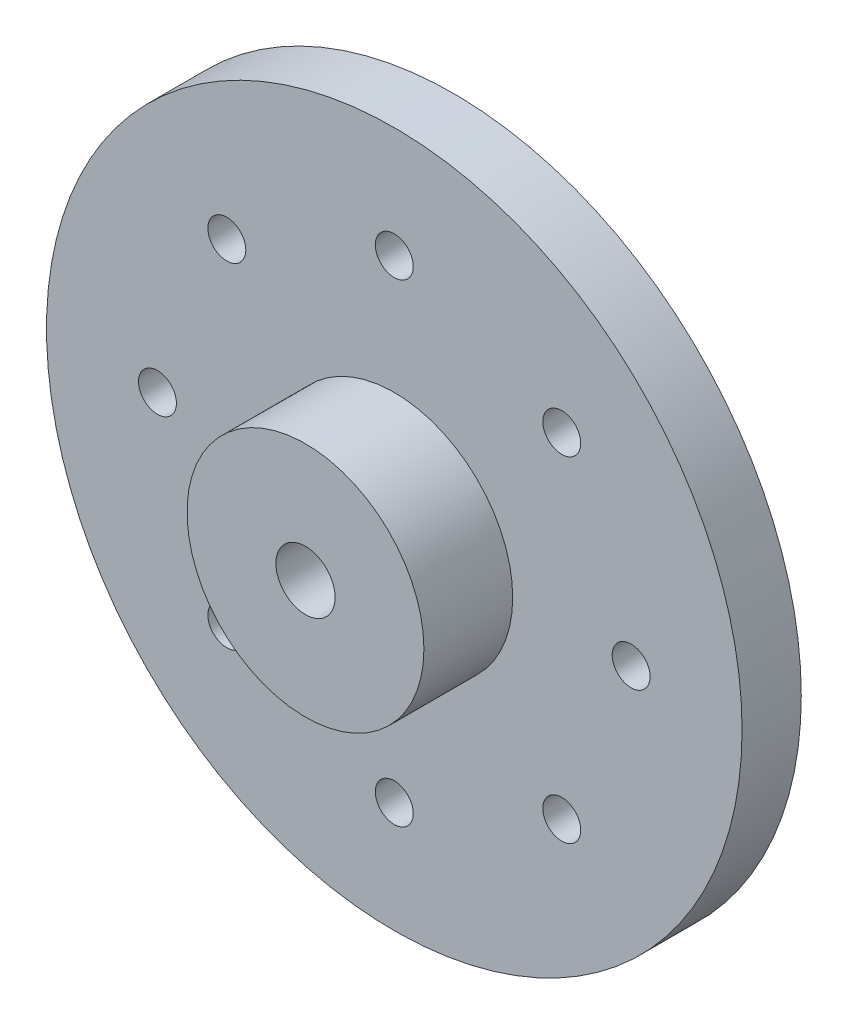
SolidWorks part; units mm, degrees
ref_plane "Front Plane" through (0, 0, 0) normal (0, 0, 1) x (1, 0, 0)
ref_plane "Top Plane" through (0, 0, 0) normal (0, 1, 0) x (1, 0, 0)
ref_plane "Right Plane" through (0, 0, 0) normal (1, 0, 0) x (0, 0, -1)
sketch "Sketch1" plane through (0, 0, 0) normal (0, 0, 1) x (1, 0, 0)
  line L0 (0, 11.7474) -> (0, -11.7474) construction
  circle A0 centre (0, 0) radius 11.7474
  circle A1 centre (0, 0) radius 2.6699
  circle A2 centre (0, 8) radius 0.6408
  circle A3 centre (5.6569, 5.6569) radius 0.6408
  circle A4 centre (8, 0) radius 0.6408
  circle A5 centre (5.6569, -5.6569) radius 0.6408
  circle A6 centre (0, -8) radius 0.6408
  circle A7 centre (-5.6569, -5.6569) radius 0.6408
  circle A8 centre (-8, 0) radius 0.6408
  circle A9 centre (-5.6569, 5.6569) radius 0.6408
  point P24 (0, 0)
  dimension "D1" = 8
  dimension "D3" = 23.4948
  dimension "D4" = 5.3397
  dimension "D5" = 1.2815
  dimension "D2" = 8
extrude "Boss-Extrude1" add sketch "Sketch1" along normal blind 2
sketch "Sketch2" plane through (0, 0, 2) normal (0, 0, 1) x (1, 0, 0)
  circle A0 centre (0, 0) radius 1
  circle A1 centre (0, 0) radius 4
  circle A2 centre (0, 0) radius 11.7474 construction
  dimension "D1" = 2
  dimension "D2" = 8
extrude "Boss-Extrude2" add sketch "Sketch2" along normal blind 3
sketch "Sketch3" plane through (0, 0, 0) normal (0, 0, -1) x (-1, 0, 0)
  circle A0 centre (0, 0) radius 2.6699
  circle A1 centre (0, 0) radius 4
extrude "Boss-Extrude3" add sketch "Sketch3" along normal blind 1
chamfer "Chamfer1" distance 0.6 angle 45 1 edges at (-4, 0, -1)
